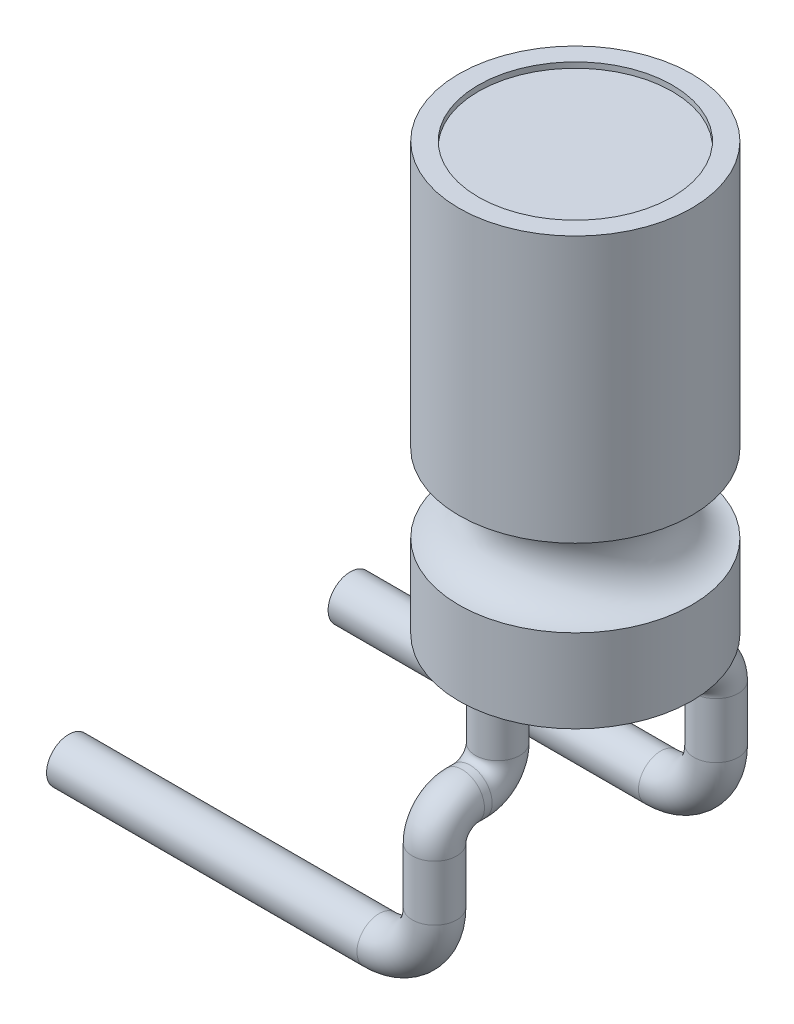
SolidWorks part; units mm, degrees
ref_plane "Face" through (0, 0, 0) normal (0, 0, 1) x (1, 0, 0)
ref_plane "Dessus" through (0, 0, 0) normal (0, 1, 0) x (1, 0, 0)
ref_plane "Droite" through (0, 0, 0) normal (1, 0, 0) x (0, 0, -1)
sketch "Esquisse1" plane through (0, 0, 0) normal (0, 0, 1) x (1, 0, 0)
  line L0 (0, 48.4017) -> (0, -33.7592) construction
  line L1 (0, 35.2164) -> (2.1, 35.2164)
  line L2 (2.1, 35.2164) -> (2.1, 30.4164)
  line L3 (2.1, 29.0164) -> (2.1, 27.5164)
  line L4 (2.1, 27.5164) -> (0, 27.5164)
  line L5 (0, 27.5164) -> (0, 35.2164)
  line L6 (9.8114, 29.7164) -> (-7.1309, 29.7164) construction
  line L7 (2.1, 25.0819) -> (2.1, 32.6721) construction
  line L8 (5.1241, 27.5164) -> (-5.6865, 27.5164) construction
  line L9 (5.1241, 29.0164) -> (-3.1767, 29.0164) construction
  arc A0 (2.1, 30.4164) -> (2.1, 29.0164) centre (2.1, 29.7164) ccw
  dimension "D4" = 0.7
  dimension "D1" = 7.7
  dimension "D2" = 2.1
  dimension "D3" = 1.5
revolve "Révolution1" add sketch "Esquisse1" angle 360 about L0
sketch "Esquisse2" plane through (0, 35.2164, 0) normal (0, 1, 0) x (-1, 0, 0)
  circle A0 centre (0, 0) radius 1.75
  dimension "D1" = 3.5
extrude "Enlèv. mat.-Extru.1" cut sketch "Esquisse2" against normal blind 0.1
sketch "Esquisse3" plane through (0, 27.5164, 0) normal (0, -1, 0) x (1, 0, 0)
  line L0 (4.0351, 0) -> (-4.283, 0) construction
  line L1 (0, 6.7464) -> (0, -6.9013) construction
  circle A0 centre (0, 1.4) radius 0.4
  dimension "D1" = 0.8
sketch "Esquisse4" plane through (0, 0, 0) normal (1, 0, 0) x (0, 0, -1)
  line L0 (-1.4, 24.8484) -> (-1.4, 29.3314) construction
  line L1 (-5.5325, 26.0164) -> (6.9013, 26.0164) construction
  line L2 (-2.54, 26.4376) -> (-2.54, 18.8472) construction
  line L3 (-8.7913, 27.5164) -> (10.5025, 27.5164) construction
  line L4 (0, 26.7733) -> (0, 22.2147) construction
  line L6 (-1.4, 27.5164) -> (-1.4, 26.5164)
  line L7 (-1.9, 26.0164) -> (-2.04, 26.0164)
  arc A0 (-1.4, 26.5164) -> (-1.9, 26.0164) centre (-1.9, 26.5164) cw
  arc A1 (-2.04, 26.0164) -> (-2.54, 25.5164) centre (-2.04, 25.5164) ccw
  dimension "D4" = 0.5
  dimension "D1" = 1.5
  dimension "D2" = 2.54
sweep "Balayage1" add profiles "Esquisse3" path "Esquisse4"
sketch "Esquisse5" plane through (0, 25.5164, 0) normal (0, -1, 0) x (1, 0, 0)
  line L0 (0, 2.8846) -> (0, 1.9) construction
  line L1 (0.1862, 2.54) -> (-0.4, 2.54) construction
  circle A0 centre (0, 2.54) radius 0.4
ref_plane "Plan1" through (0, 0, 2.54) normal (0, 0, 1) x (1, 0, 0)
sketch "Esquisse6" plane through (0, 0, 2.54) normal (0, 0, 1) x (1, 0, 0)
  line L0 (0, 25.7821) -> (0, 22.579) construction
  line L1 (1.0149, 23.5164) -> (-9.4986, 23.5164) construction
  line L2 (9.4986, 25.5164) -> (-9.4986, 25.5164) construction
  line L3 (-2.6, 27.2212) -> (-2.6, 21.8479) construction
  line L4 (-6.6, 21.8479) -> (-6.6, 27.2212) construction
  line L5 (0, 25.5164) -> (0, 24.5164)
  line L6 (-1, 23.5164) -> (-6.6, 23.5164)
  arc A0 (0, 24.5164) -> (-1, 23.5164) centre (-1, 24.5164) cw
  point P15 (-6.6, 23.5164)
  point P16 (0, 25.5164)
  dimension "D3" = 1
  dimension "D1" = 4
  dimension "D2" = 2
sweep "Balayage2" add profiles "Esquisse5" path "Esquisse6"
ref_plane "Plan2" through (0, 0, 0) normal (0, 0, 1) x (1, 0, 0)
mirror "Symétrie1" about plane through (0, 0, 0) normal (0, 0, 1) of "Balayage2", "Balayage1"
